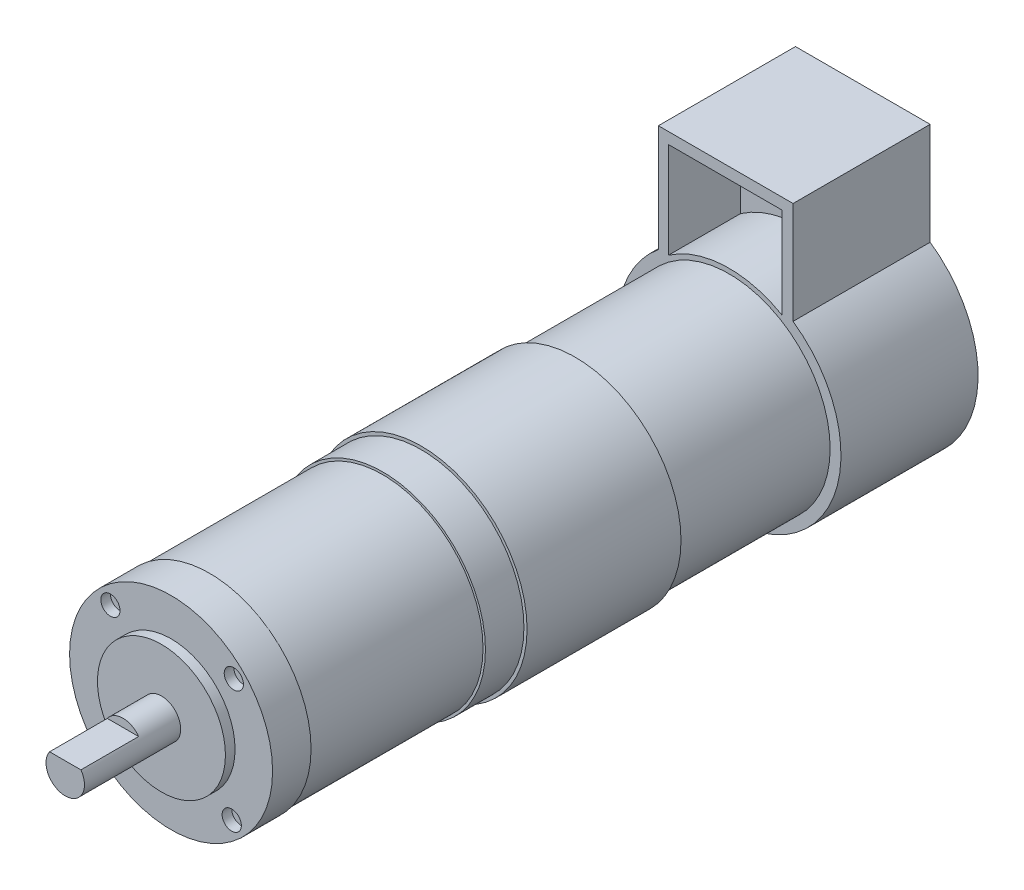
SolidWorks part; units mm, degrees
material "1060 Alloy"
ref_plane "Front Plane" through (0, 0, 0) normal (0, 0, 1) x (1, 0, 0)
ref_plane "Top Plane" through (0, 0, 0) normal (0, 1, 0) x (1, 0, 0)
ref_plane "Right Plane" through (0, 0, 0) normal (1, 0, 0) x (0, 0, -1)
ref_plane "Plane1" through (0, 0, 0) normal (0, 0, -1) x (-1, 0, 0)
sketch "Sketch1" plane through (0, 0, 0) normal (0, 0, -1) x (-1, 0, 0)
  line L0 (14.7074, 18.0071) -> (14.7074, 19.0754)
  line L1 (14.7074, 19.0754) -> (-13.2926, 19.0754)
  arc A0 (-13.2926, 19.0754) -> (14.7074, 18.0071) centre (0, 0) ccw
extrude "Boss-Extrude1" add sketch "Sketch1" against normal blind 28.5
sketch "Sketch2" plane through (0, 0, 28.5) normal (0, 0, 1) x (1, 0, 0)
  circle A0 centre (0, 0) radius 21
extrude "Boss-Extrude2" add sketch "Sketch2" along normal blind 32
ref_plane "Plane2" through (0, 0, 60.5) normal (0, 0, -1) x (-1, 0, 0)
sketch "Sketch3" plane through (0, 0, 60.5) normal (0, 0, -1) x (-1, 0, 0)
  circle A0 centre (0, 0) radius 22
extrude "Boss-Extrude3" add sketch "Sketch3" against normal blind 32
sketch "Sketch4" plane through (0, 0, 92.5) normal (0, 0, 1) x (1, 0, 0)
  circle A0 centre (0, 0) radius 21.35
extrude "Boss-Extrude4" add sketch "Sketch4" along normal blind 8
sketch "Sketch5" plane through (0, 0, 100.5) normal (0, 0, 1) x (1, 0, 0)
  circle A0 centre (0, 0) radius 20.85
extrude "Boss-Extrude5" add sketch "Sketch5" along normal blind 36
sketch "Sketch6" plane through (0, 19.0754, 0) normal (0, 1, 0) x (-1, 0, 0)
  line L0 (14.7074, 28.5) -> (14.7074, 0)
  line L1 (14.7074, 0) -> (-13.2926, 0)
  line L2 (-13.2926, 0) -> (-13.2926, 28.5)
  line L3 (-13.2926, 28.5) -> (14.7074, 28.5)
extrude "Boss-Extrude6" add sketch "Sketch6" along normal blind 21.2246
ref_plane "Plane3" through (0, 0, 136.5) normal (0, 0, -1) x (-1, 0, 0)
sketch "Sketch7" plane through (0, 0, 136.5) normal (0, 0, -1) x (-1, 0, 0)
  circle A0 centre (0, 0) radius 21.1
extrude "Boss-Extrude7" add sketch "Sketch7" against normal blind 8
sketch "Sketch8" plane through (0, 0, 144.5) normal (0, 0, 1) x (1, 0, 0)
  circle A0 centre (0, 0) radius 13.3
extrude "Boss-Extrude8" add sketch "Sketch8" along normal blind 2
sketch "Sketch9" plane through (0, 0, 146.5) normal (0, 0, 1) x (1, 0, 0)
  circle A0 centre (0, 0) radius 4
extrude "Boss-Extrude9" add sketch "Sketch9" along normal blind 20
sketch "Sketch10" plane through (0, 0, 166.5) normal (0, 0, 1) x (1, 0, 0)
  line L0 (-3.2554, 2.3243) -> (3.2554, 2.3243)
  arc A0 (3.2554, 2.3243) -> (-3.2554, 2.3243) centre (0, 0) ccw
extrude "Cut-Extrude1" cut sketch "Sketch10" against normal blind 12
sketch "Sketch11" plane through (0, 0, 28.5) normal (0, 0, 1) x (1, 0, 0)
  line L0 (10.9604, 19.0754) -> (10.9604, 37.9656)
  line L1 (10.9604, 37.9656) -> (-12.639, 37.9656)
  line L2 (-12.639, 37.9656) -> (-12.639, 18.0071)
  arc A0 (-12.639, 18.0071) -> (10.9604, 19.0754) centre (0, 0) cw
extrude "Cut-Extrude2" cut sketch "Sketch11" against normal blind 15
hole_wizard "Ø4.0 (4) Diameter Hole1" positions "Sketch13" profile "Sketch12" hole size "Ø4.0" standard "ANSI Metric"
sketch "Sketch13" plane through (0, 0, 144.5) normal (0, 0, 1) x (1, 0, 0)
  point P0 (-13.044, -12.6109)
  point P1 (12.6109, -13.044)
  point P2 (13.044, 12.6109)
  point P3 (-12.6109, 13.044)
sketch "Sketch12" plane through (-13.044, -12.6109, 144.5) normal (1, 0, 0) x (0, -1, 0)
  line L0 (0, 0) -> (0, 2)
  line L1 (0, 2) -> (2, 2)
  line L2 (2, 2) -> (2, 0)
  line L5 (2, 0) -> (0, 0)
  line L10 (0, 2) -> (-2, 2) construction
  line L11 (0, -6.35) -> (0, 107.95) construction
  dimension "Hole Dia." = 4
  dimension "Hole Depth" = 2
  dimension "Drill Angle" = 180
